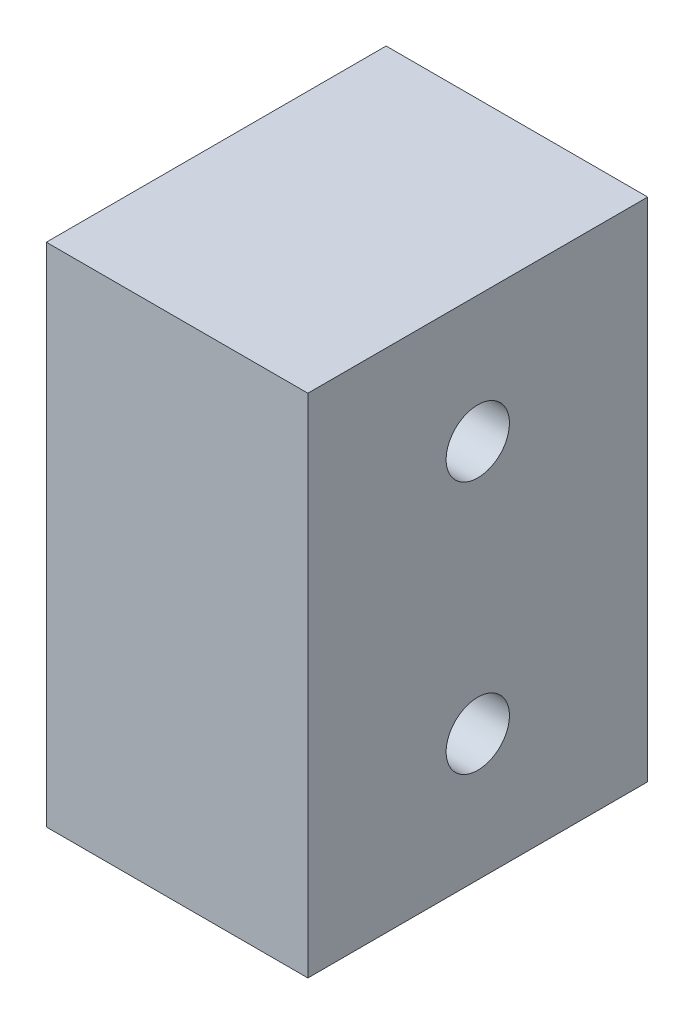
SolidWorks part; units mm, degrees
ref_plane "Front Plane" through (0, 0, 0) normal (1, 0, 0) x (0, 1, 0)
ref_plane "Top Plane" through (0, 0, 0) normal (0, 0, 1) x (0, 1, 0)
ref_plane "Right Plane" through (0, 0, 0) normal (0, 1, 0) x (-1, 0, 0)
sketch "Sketch1" plane through (0, 0, 0) normal (1, 0, 0) x (0, 1, 0)
  line L1 (10, 6.71) -> (-10, 6.71)
  line L2 (10, 6.71) -> (10, -6.71)
  line L3 (10, -6.71) -> (-10, -6.71)
  line L4 (-10, 6.71) -> (-10, -6.71)
  line L5 (10, 6.71) -> (-10, -6.71) construction
  line L6 (10, -6.71) -> (-10, 6.71) construction
  point P0 (0, 0)
  dimension "D1" = 20
  dimension "D2" = 13.42
extrude "Boss-Extrude1" add sketch "Sketch1" along normal blind 10.33
ref_plane "Plane1" through (10.33, 0, 0) normal (1, 0, 0) x (0, 0, -1)
sketch "Sketch2" plane through (10.33, 0, 0) normal (1, 0, 0) x (0, 0, -1)
  line L0 (-6.71, 0) -> (6.71, 0) construction
  line L1 (-6.71, 10) -> (-6.71, -10) construction
  line L2 (6.71, -10) -> (6.71, 10) construction
  line L3 (0, 5) -> (0, -5) construction
  circle A0 centre (0, 5) radius 1.25
  circle A1 centre (0, -5) radius 1.25
  point P9 (0, 0)
  dimension "D1" = 2.5
  dimension "D2" = 2.5
  dimension "D3" = 10
extrude "Cut-Extrude1" cut sketch "Sketch2" against normal blind 10.33
